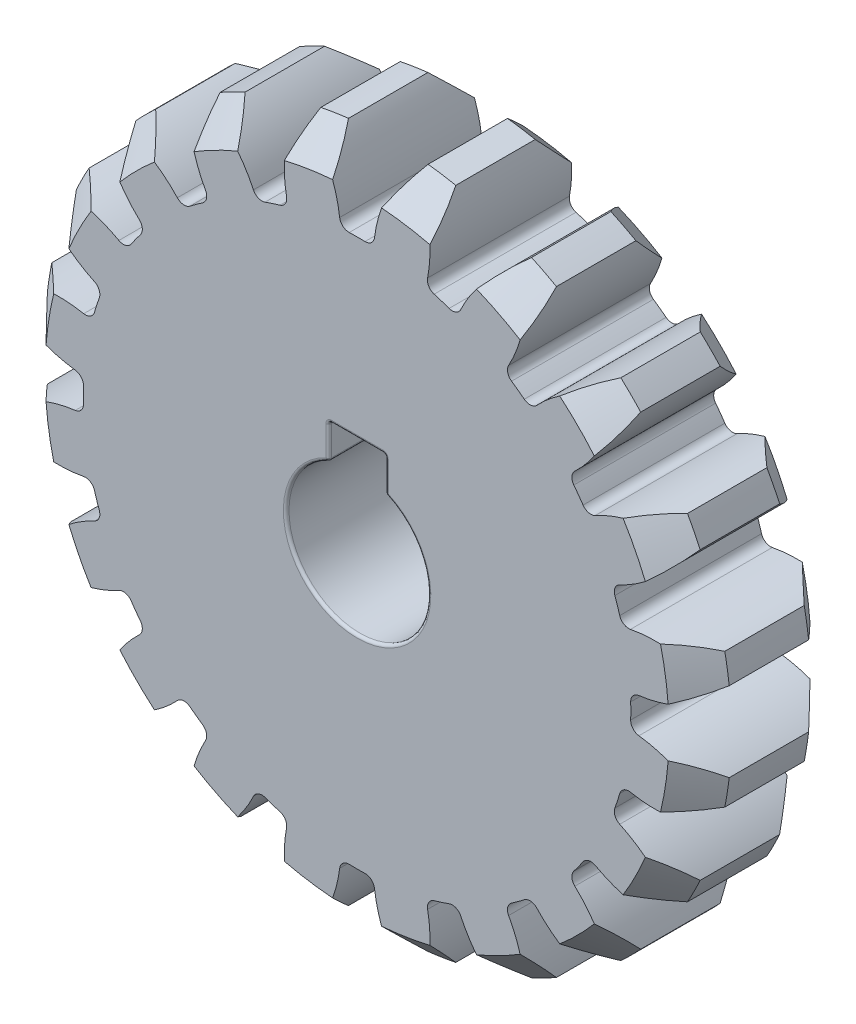
SolidWorks part; units mm, degrees
ref_plane "Front Plane" through (0, 0, 0) normal (0, 0, 1) x (1, 0, 0)
ref_plane "Top Plane" through (0, 0, 0) normal (0, 1, 0) x (1, 0, 0)
ref_plane "Right Plane" through (0, 0, 0) normal (1, 0, 0) x (0, 0, -1)
sketch "Sketch1" plane through (0, 0, 0) normal (0, 0, 1) x (1, 0, 0)
  circle A0 centre (0, 0) radius 22 construction
  circle A1 centre (0, 0) radius 24.2
  dimension "D1" = 44
  dimension "D2" = 48.4
extrude "Boss-Extrude1" add sketch "Sketch1" along normal mid plane 10
sketch "Sketch2" plane through (0, 0, 0) normal (0, 0, 1) x (1, 0, 0)
  line L0 (0, 0) -> (0, 24.2) construction
  line L1 (0, 0) -> (7.4782, 23.0156) construction
  line L2 (0, 0) -> (3.7857, 23.9021) construction
  line L3 (-1.1717, 19.2644) -> (0, 0) construction
  line L4 (-1.7261, 21.9322) -> (1.7261, 21.9322) construction
  line L5 (1.7261, 21.9322) -> (5.1358, 21.3921) construction
  line L6 (-2.5042, 24.0701) -> (0, 17.1898) construction
  circle A0 centre (0, 0) radius 19.8 construction
  circle A2 centre (0, 0) radius 24.2 construction
  arc A3 (-2.8061, 24.0368) -> (-1.1717, 19.2644) centre (-10.6375, 18.6887) cw
  circle A4 centre (0, 0) radius 24.2 construction
  arc A5 (2.8061, 24.0368) -> (1.1717, 19.2644) centre (10.6375, 18.6887) ccw
  circle A6 centre (0, 0) radius 22 construction
  arc A7 (1.1717, 19.2644) -> (-1.1717, 19.2644) centre (0, 0) ccw
  arc A8 (2.8061, 24.0368) -> (-2.8061, 24.0368) centre (0, 0) ccw
  dimension "D1" = 18
  dimension "D2" = 4.4
  dimension "D4" = 20
  dimension "D3" = 0.5
extrude "Cut-Extrude1" cut sketch "Sketch2" against normal through all both and the other way through all contours A5 A8 A3 A7
fillet "Fillet1" radius 0.66 2 edges at (1.1717, 19.2644, 0) (-1.1717, 19.2644, 0)
chamfer "Chamfer1" distance 2.2 angle 45 2 edges at (0, -24.2, -5) (0, -24.2, 5)
pattern_circular "CirPattern1" count 20 over 360 about axis through (0, 0, 0) along (0, 0, 1) of "Fillet1", "Cut-Extrude1"
sketch "Sketch3" plane through (0, 0, 5) normal (0, 0, 1) x (1, 0, 0)
  line L2 (-2, 4.5826) -> (-2, 7)
  line L3 (-2, 7) -> (2, 7)
  line L4 (2, 4.5826) -> (2, 7)
  arc A0 (-2, 4.5826) -> (2, 4.5826) centre (0, 0) ccw
  point P3 (0, 5)
  point P5 (0, 7)
  dimension "D1" = 10
  dimension "D2" = 2
  dimension "D3" = 4
extrude "Cut-Extrude2" cut sketch "Sketch3" against normal through all
fillet "Fillet2" radius 0.2 12 edges at (0, -5, 5) (0, -5, -5) (-2, 4.5826, 0) (2, 4.5826, 0) (0, 7, -5) (0, 7, 5) (-2, 7, 0) (-2, 5.7913, -5) (-2, 5.7913, 5) (2, 5.7913, -5) (2, 7, 0) (2, 5.7913, 5)
sketch "Sketch5" plane through (0, 0, 0) normal (0, 0, 1) x (1, 0, 0)
  circle A0 centre (0, 0) radius 22
equation "\"Module\"= 2.2"
equation "\"Number of Teeth\"= 20'Number of Teeth"
equation "\"Pressure Angle\"= 20"
equation "\"D1@Sketch1\"=\"Module\" * \"Number of Teeth\""
equation "\"D2@Sketch1\"=( \"Number of Teeth\" + 2) * \"Module\""
equation "\"D1@Sketch2\"=360 / \"Number of Teeth\""
equation "\"D2@Sketch2\"= \"Module\" * 2"
equation "\"D4@Sketch2\"=\"Pressure Angle\""
equation "\"D1@Fillet1\"=0.3 * \"Module\""
equation "\"D1@CirPattern1\"= \"Number of Teeth\""
equation "\"D1@Chamfer1\"= \"Module\""
equation "\"Gear Thickness\"= 10"
equation "\"D1@Boss-Extrude1\"= \"Gear Thickness\""
